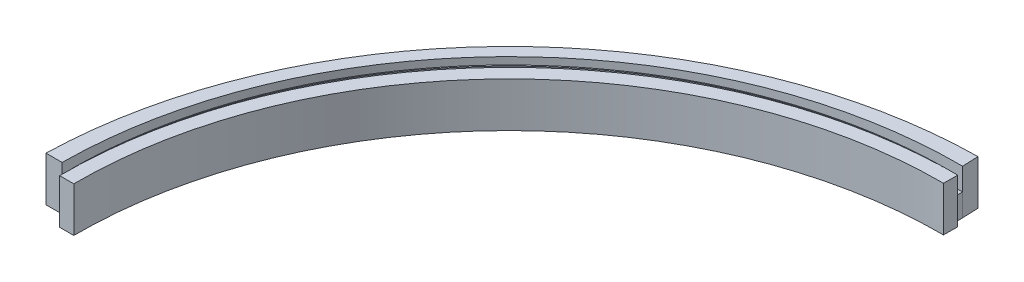
SolidWorks part; units mm, degrees
material "Natural Rubber"
ref_plane "Front Plane" through (0, 0, 0) normal (0, 0, 1) x (1, 0, 0)
ref_plane "Top Plane" through (0, 0, 0) normal (0, 1, 0) x (1, 0, 0)
ref_plane "Right Plane" through (0, 0, 0) normal (1, 0, 0) x (0, 0, -1)
sketch "Sketch1" plane through (0, 0, 0) normal (0, 0, 1) x (1, 0, 0)
  line L1 (0, 0) -> (2.06, 0)
  line L2 (0, 0) -> (0, 6.53)
  line L3 (0, 6.53) -> (2.06, 6.53)
  line L4 (2.06, 0) -> (2.06, 6.53)
  dimension "D1" = 6.53
  dimension "D2" = 2.06
sketch "Sketch2" plane through (0, 0, 0) normal (0, 1, 0) x (1, 0, 0)
  line L0 (-55, 0) -> (55, 0) construction
  arc A0 (2.06, 0) -> (65.4158, 63.4965) centre (65.209, 0.3469) cw
  dimension "D1" = 63.15
sweep "Sweep1" add profiles "Sketch1" path "Sketch2"
ref_plane "Plane1" through (0, 0, -1.85) normal (0, 0, 1) x (1, 0, 0)
sketch "Sketch3" plane through (0, 0, -1.85) normal (0, 0, 1) x (1, 0, 0)
  line L1 (0, 0) -> (-1.5, 0)
  line L2 (0, 0) -> (0, 6.53)
  line L3 (0, 6.53) -> (-1.5, 6.53)
  line L4 (-1.5, 0) -> (-1.5, 6.53)
  dimension "D1" = 1.5
  dimension "D2" = 6.53
ref_plane "Plane2" through (63.0042, 0, 0.5523) normal (1, 0, 0.0088) x (0.0088, 0, -1)
sketch "Sketch4" plane through (0, 0, 0) normal (0, 1, 0) x (1, 0, 0)
  line L4 (0, 1.85) -> (-1.5, 1.85) construction
  arc A2 (-2.34, 1.85) -> (64.643, 67.885) centre (64.643, 0.8953) cw
  dimension "D1" = 66.9898
sweep "Sweep2" add profiles "Sketch3" path "Sketch4"
sketch "Sketch6" plane through (0, 0, -1.85) normal (0, 0, 1) x (1, 0, 0)
  line L0 (-1.5, 0) -> (-3.84, 0)
  line L1 (-3.84, 0) -> (-3.84, 6.53)
  line L2 (-3.84, 6.53) -> (-1.5, 6.53)
  line L6 (-1.5, 6.53) -> (-1.5, 0)
  dimension "D1" = 2.34
  dimension "D2" = 2.34
  dimension "D3" = 6.53
sketch "Sketch7" plane through (0, 6.53, 0) normal (0, 1, 0) x (1, 0, 0)
  arc A0 (-1.5, 1.85) -> (64.6549, 67.0451) centre (65.4658, 0.0603) cw
sweep "Sweep3" add profiles "Sketch6" path "Sketch7"
sketch "Sketch8" plane through (0, 6.53, 0) normal (0, 1, 0) x (1, 0, 0)
  line L0 (0, 1.85) -> (-1.4906, 1.85)
  line L1 (64.6762, 65.5547) -> (64.6549, 67.0451)
  arc A0 (0, 1.85) -> (64.6762, 65.5547) centre (64.1904, 1.3643) cw
  arc A1 (-1.4906, 1.85) -> (64.6549, 67.0451) centre (64.1797, 1.3748) cw
  dimension "D1" = 1.4906
extrude "Cut-Extrude1" cut sketch "Sketch8" against normal blind 3.25
scale "Scale1" scale about centroid uniform scaling yes scale factor 0.5
